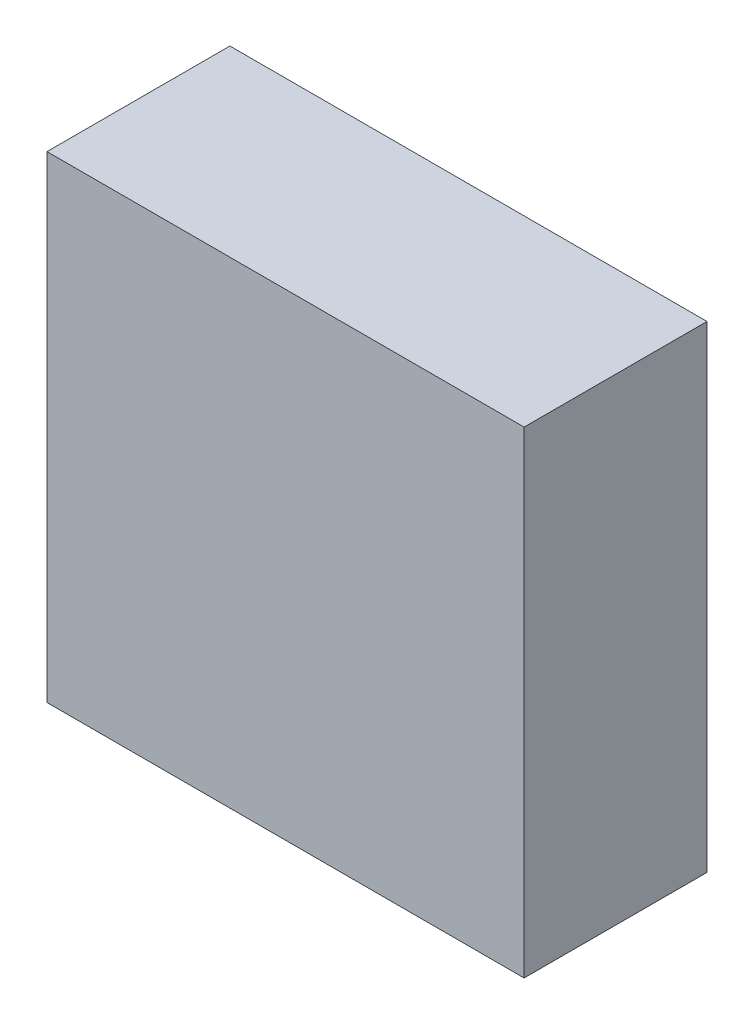
SolidWorks part; units mm, degrees
ref_plane "前视基准面" through (0, 0, 0) normal (0, 0, 1) x (1, 0, 0)
ref_plane "上视基准面" through (0, 0, 0) normal (0, 1, 0) x (1, 0, 0)
ref_plane "右视基准面" through (0, 0, 0) normal (1, 0, 0) x (0, 0, -1)
sketch "草图1" plane through (0, 0, 0) normal (0, 0, 1) x (1, 0, 0)
  line L0 (17.2496, 9.3126) -> (23.2496, 9.3126)
  line L1 (17.2496, 15.3126) -> (23.2496, 15.3126)
  line L2 (17.2496, 15.3126) -> (17.2496, 9.3126)
  line L3 (23.2496, 15.3126) -> (23.2496, 9.3126)
  dimension "D1" = 6
  dimension "D2" = 6
extrude "凸台-拉伸1" add sketch "草图1" along normal blind 2.3
